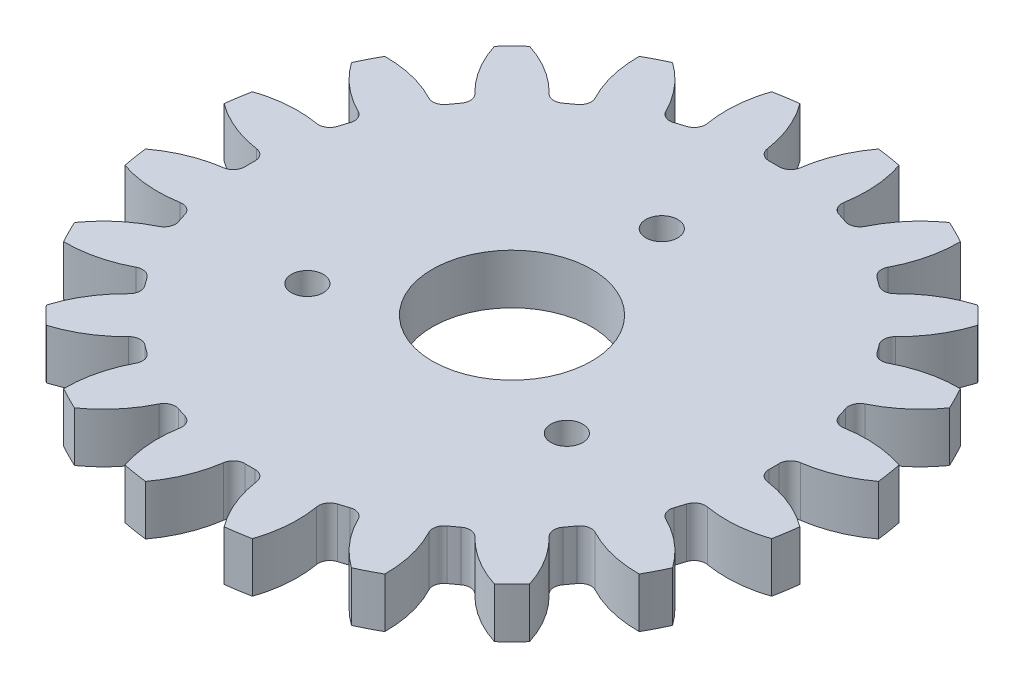
SolidWorks part; units mm, degrees
material "Acrylic (Medium-high impact)"
ref_plane "Front Plane" through (0, 0, 0) normal (0, 0, 1) x (1, 0, 0)
ref_plane "Top Plane" through (0, 0, 0) normal (0, 1, 0) x (1, 0, 0)
ref_plane "Right Plane" through (0, 0, 0) normal (1, 0, 0) x (0, 0, -1)
sketch "Sketch2" plane through (0, 0, 0) normal (0, 1, 0) x (1, 0, 0)
  circle A0 centre (0, 0) radius 33
  circle A1 centre (0, 0) radius 7.975
  dimension "D1" = 15.95
  dimension "D2" = 66
extrude "Boss-Extrude1" add sketch "Sketch2" along normal blind 5
sketch "Sketch3" plane through (0, 5, 0) normal (0, 1, 0) x (1, 0, 0)
  line L0 (0, 0) -> (0, 33) construction
  line L1 (-1.5456, 26.2045) -> (0, 0) construction
  line L2 (0, 23.449) -> (4.1879, 11.9429) construction
  arc A0 (1.5456, 26.2045) -> (-1.5456, 26.2045) centre (0, 0) ccw
  arc A1 (2.3538, 29.9075) -> (-2.3538, 29.9075) centre (0, 0) ccw construction
  arc A2 (3.9334, 32.7647) -> (-3.9334, 32.7647) centre (0, 0) ccw
  circle A3 centre (0, 0) radius 33 construction
  arc A5 (-3.9334, 32.7647) -> (-1.5456, 26.2045) centre (-13.7254, 25.4861) cw
  arc A6 (3.9334, 32.7647) -> (1.5456, 26.2045) centre (13.7254, 25.4861) ccw
  point P16 (-2.2603, 29.659)
  dimension "D1" = 60
  dimension "D2" = 6.75
  dimension "D3" = 20
  dimension "D4" = 4.7124
extrude "Cut-Extrude1" cut sketch "Sketch3" against normal through all
fillet "Fillet1" radius 1.14 2 edges at (1.5456, 2.5, -26.2045) (-1.5456, 2.5, -26.2045)
pattern_circular "CirPattern1" count 20 over 360 about axis through (0, 0, 0) along (0, 1, 0) of "Cut-Extrude1", "Fillet1"
sketch "Sketch4" plane through (0, 0, 0) normal (0, -1, 0) x (1, 0, 0)
  line L0 (0, 0) -> (0, 15) construction
  line L1 (-3.8823, 14.4889) -> (0, 0) construction
  line L2 (0, 0) -> (3.8823, 14.4889) construction
  circle A0 centre (0, 0) radius 15 construction
  arc A5 (-3.8823, 14.4889) -> (3.8823, 14.4889) centre (0, 0) cw construction
  arc A6 (4.2964, 16.0344) -> (-4.2964, 16.0344) centre (0, 0) ccw
  arc A7 (3.4682, 12.9434) -> (-3.4682, 12.9434) centre (0, 0) ccw
  arc A8 (3.4682, 12.9434) -> (4.2964, 16.0344) centre (3.8823, 14.4889) ccw
  arc A9 (-4.2964, 16.0344) -> (-3.4682, 12.9434) centre (-3.8823, 14.4889) ccw
  arc A10 (14.4889, -3.8823) -> (10.6066, -10.6066) centre (0, 0) cw construction
  arc A11 (11.738, -11.738) -> (16.0344, -4.2964) centre (0, 0) ccw
  arc A12 (9.4752, -9.4752) -> (12.9434, -3.4682) centre (0, 0) ccw
  arc A13 (9.4752, -9.4752) -> (11.738, -11.738) centre (10.6066, -10.6066) ccw
  arc A14 (16.0344, -4.2964) -> (12.9434, -3.4682) centre (14.4889, -3.8823) ccw
  arc A15 (-10.6066, -10.6066) -> (-14.4889, -3.8823) centre (0, 0) cw construction
  arc A16 (-16.0344, -4.2964) -> (-11.738, -11.738) centre (0, 0) ccw
  arc A17 (-12.9434, -3.4682) -> (-9.4752, -9.4752) centre (0, 0) ccw
  arc A18 (-12.9434, -3.4682) -> (-16.0344, -4.2964) centre (-14.4889, -3.8823) ccw
  arc A19 (-11.738, -11.738) -> (-9.4752, -9.4752) centre (-10.6066, -10.6066) ccw
  point P5 (0, 15)
  point P19 (12.9904, -7.5)
  point P26 (-12.9904, -7.5)
  point P31 (0, 0)
  dimension "D1" = 30
  dimension "D3" = 30
  dimension "D2" = 1.6
  dimension "D4" = 3
extrude "Cut-Extrude2" [suppressed] cut sketch "Sketch4" against normal through all
sketch "Sketch6" plane through (0, 5, 0) normal (0, 1, 0) x (1, 0, 0)
  line L0 (0, 0) -> (0, 15) construction
  circle A0 centre (0, 15) radius 1.6
  circle A1 centre (12.9904, -7.5) radius 1.6
  circle A2 centre (-12.9904, -7.5) radius 1.6
  dimension "D1" = 3.2
  dimension "D2" = 15
  dimension "D3" = 3
extrude "Cut-Extrude3" cut sketch "Sketch6" against normal through all
equation "\"No. of teeth\"= 20"
equation "\"Module\"= 3"
equation "\"Bore diameter\"= 15.95"
equation "\"Pressure angle\"= 20"
equation "\"Outer diameter\"= ( \"No. of teeth\" + 2 ) * \"Module\""
equation "\"Pitch diameter\"= \"No. of teeth\" * \"Module\""
equation "\"Backlash\"= 0"
equation "\"Arc length\"= ( ( \"Module\" * pi ) / 2 ) + \"Backlash\""
equation "\"Fillet radius\"= 0.38 * \"Module\""
equation "\"Tooth depth\"= IIF ( \"Module\" <= 1.25 , \"Module\" * 2.4 , \"Module\" * 2.25 )"
equation "\"D1@Sketch2\"=\"Bore diameter\""
equation "\"D2@Sketch2\"=\"Outer diameter\""
equation "\"D1@Sketch3\"=\"Pitch diameter\""
equation "\"D2@Sketch3\"=\"Tooth depth\""
equation "\"D3@Sketch3\"=\"Pressure angle\""
equation "\"D4@Sketch3\"=\"Arc length\""
equation "\"D1@Fillet1\"=\"Fillet radius\""
equation "\"D1@CirPattern1\"=\"No. of teeth\""
equation "\"Gear thickness\"= 5"
equation "\"D1@Boss-Extrude1\"=\"Gear thickness\""
